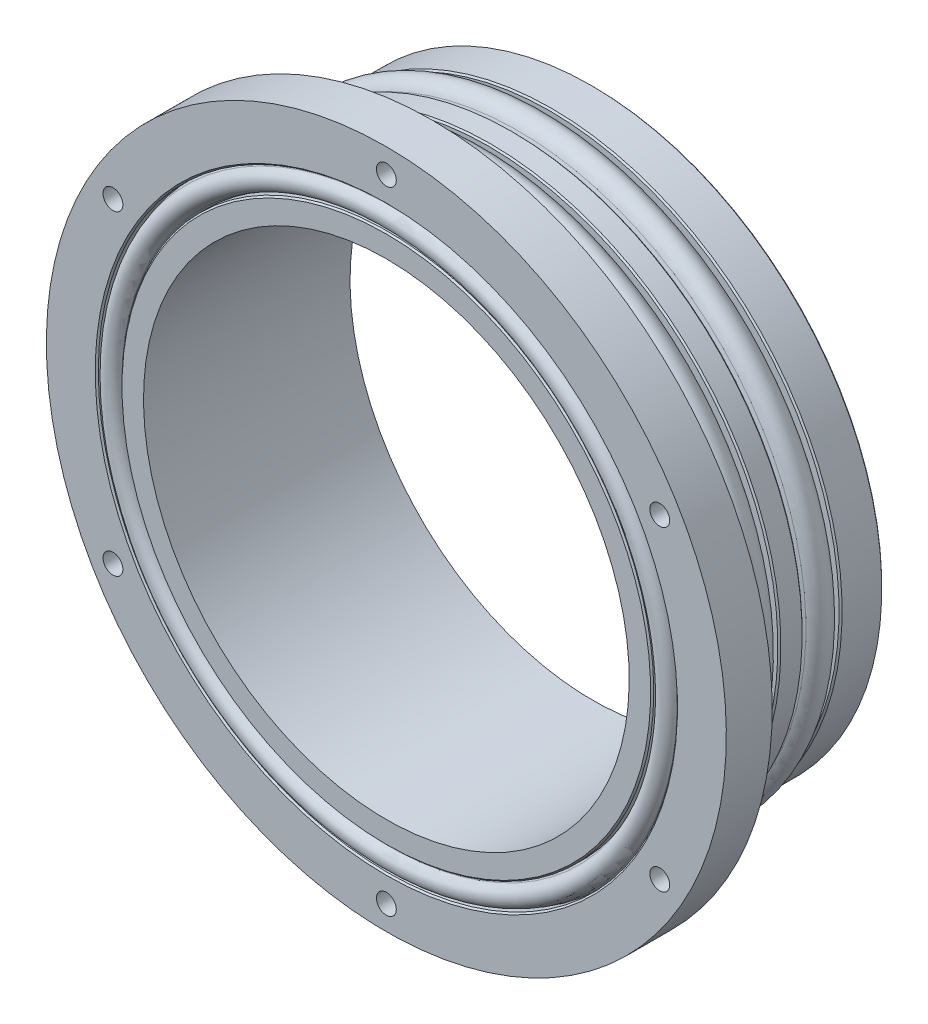
SolidWorks part; units mm, degrees
material "1060 Alloy"
ref_plane "Front Plane" through (0, 0, 0) normal (0, 0, 1) x (1, 0, 0)
ref_plane "Top Plane" through (0, 0, 0) normal (0, 1, 0) x (1, 0, 0)
ref_plane "Right Plane" through (0, 0, 0) normal (1, 0, 0) x (0, 0, -1)
sketch "Sketch1" plane through (0, 0, 0) normal (1, 0, 0) x (0, 0, -1)
  line L0 (0, 0) -> (0, 38.227) construction
  line L1 (0, 37.973) -> (-5.587, 37.973)
  line L2 (-21, 37.973) -> (-21, 44.45)
  line L3 (-21, 44.45) -> (-27, 44.45)
  line L4 (-27, 44.45) -> (-27, 37.8587)
  line L5 (-27, 31.75) -> (0, 31.75)
  line L6 (0, 31.75) -> (0, 37.973)
  line L7 (-18.413, 37.973) -> (-21, 37.973)
  line L8 (-10.413, 37.973) -> (-13.587, 37.973)
  line L9 (0, 0) -> (-27, 0) construction
  line L10 (-27, 0) -> (-27, 31.75) construction
  line L11 (-18.413, 37.973) -> (-18.413, 35.2806)
  line L12 (-18.413, 35.2806) -> (-13.587, 35.2806)
  line L13 (-13.587, 35.2806) -> (-13.587, 37.973)
  line L14 (-10.413, 37.973) -> (-10.413, 35.2806)
  line L15 (-10.413, 35.2806) -> (-5.587, 35.2806)
  line L16 (-5.587, 35.2806) -> (-5.587, 37.973)
  line L17 (0, 38.227) -> (-21, 38.227) construction
  line L18 (-16, 38.227) -> (-16, 38.8112) construction
  line L19 (-21, 37.973) -> (0, 37.973) construction
  line L20 (-27, 34.7599) -> (-24.9426, 34.7599)
  line L21 (-24.9426, 34.7599) -> (-24.9426, 37.8587)
  line L22 (-24.9426, 37.8587) -> (-27, 37.8587)
  line L23 (-27, 34.7599) -> (-27, 31.75)
  line L24 (0, 36.3615) -> (-4, 36.3615) construction
  line L25 (-4, 36.3615) -> (-4, 33.3615) construction
  line L26 (-4, 33.3615) -> (0, 33.3615) construction
  line L27 (-4, 34.8615) -> (0, 34.8615) construction
  circle A0 centre (-16, 37.0459) radius 1.7653 construction
  circle A1 centre (-8, 37.0459) radius 1.7653 construction
  point P2 (-8, 35.2806)
  point P21 (-16, 35.2806)
  dimension "D4" = 3.5306
  dimension "D12" = 2.6924
  dimension "D1" = 38.227
  dimension "D2" = 75.946
  dimension "D3" = 31.75
  dimension "D5" = 21
  dimension "D6" = 6
  dimension "D7" = 88.9
  dimension "D8" = 4.826
  dimension "D9" = 8
  dimension "D10" = 8
  dimension "D11" = 70.5612
  dimension "D13" = 2.0574
  dimension "D14" = 37.973
  dimension "D15" = 2.9464
  dimension "D16" = 0
  dimension "D17" = 0.508
  dimension "D18" = 70.5612
  dimension "D19" = 3.0988
  dimension "D20" = 69.5198
  dimension "D21" = 3.0099
  dimension "D22" = 3
  dimension "D23" = 4
revolve "Revolve1" add sketch "Sketch1" angle 360 about L9
sketch "Sketch2" plane through (0, 0, 27) normal (0, 0, 1) x (1, 0, 0)
  circle A0 centre (0, 41.275) radius 1.3
  circle A1 centre (0, 0) radius 44.45 construction
  circle A2 centre (35.7452, 20.6375) radius 1.3
  circle A3 centre (35.7452, -20.6375) radius 1.3
  circle A4 centre (0, -41.275) radius 1.3
  circle A5 centre (-35.7452, -20.6375) radius 1.3
  circle A6 centre (-35.7452, 20.6375) radius 1.3
  point P17 (0, 0)
  dimension "D1" = 2.6
  dimension "D2" = 3.175
  dimension "D3" = 6
extrude "Cut-Extrude1" cut sketch "Sketch2" against normal up to surface (6 mm away) up to face at (0, 44.45, 21)
chamfer "Chamfer1" distance 0.2 angle 45 7 edges at (0, 37.973, 18.413) (0, 37.973, 5.587) (0, 37.973, 10.413) (0, 37.973, 13.587) (0, 37.973, 0) (0, 37.8587, 27) (0, 34.7599, 27)
sketch "Sketch3" plane through (0, 0, 0) normal (0, 0, -1) x (-1, 0, 0)
  line L0 (-34.29, 0) -> (0, 0) construction
  line L1 (0, 0) -> (0, 34.29) construction
  line L2 (0, 0) -> (34.29, 0) construction
  line L3 (0, -34.29) -> (0, 0) construction
  circle A0 centre (-34.29, 0) radius 1.3
  circle A1 centre (0, 34.29) radius 1.3
  circle A2 centre (34.29, 0) radius 1.3
  circle A3 centre (0, -34.29) radius 1.3
  circle A4 centre (-34.29, 0) radius 2.75 construction
  dimension "D2" = 5.5
  dimension "D3" = 2.6
  dimension "D1" = 68.58
extrude "Cut-Extrude2" cut sketch "Sketch3" against normal blind 4
sketch "Sketch4" plane through (0, 0, 0) normal (1, 0, 0) x (0, 0, -1)
  line L0 (-18.413, 36.0426) -> (-13.587, 36.0426) construction
  line L1 (-13.587, 36.0426) -> (-14.2347, 37.626)
  line L2 (-14.2347, 37.626) -> (-17.7653, 37.626) construction
  line L3 (-17.7653, 37.626) -> (-18.413, 36.0426)
  line L4 (-16, 38.8112) -> (-16, 36.0426) construction
  line L5 (-18.413, -37.773) -> (-18.413, 37.773) construction
  line L6 (-13.587, 37.773) -> (-13.587, -37.773) construction
  line L7 (-18.413, 36.0426) -> (-18.413, 35.2806)
  line L8 (-18.413, -35.2806) -> (-18.413, 35.2806) construction
  line L9 (-18.413, 35.2806) -> (-13.587, 35.2806)
  line L10 (-13.587, 35.2806) -> (-13.587, 36.0426)
  line L11 (-5.587, 37.773) -> (-5.587, -37.773) construction
  line L12 (-10.413, 36.0426) -> (-5.587, 36.0426) construction
  line L13 (-5.587, 36.0426) -> (-6.2347, 37.626)
  line L14 (-6.2347, 37.626) -> (-9.7653, 37.626) construction
  line L15 (-9.7653, 37.626) -> (-10.413, 36.0426)
  line L16 (-8, 38.8112) -> (-8, 36.0426) construction
  line L17 (-10.413, 36.0426) -> (-10.413, 35.2806)
  line L18 (-10.413, 35.2806) -> (-5.587, 35.2806)
  line L19 (-5.587, 35.2806) -> (-5.587, 36.0426)
  line L20 (-5.587, 35.2806) -> (-5.587, -35.2806) construction
  line L21 (-10.413, -37.773) -> (-10.413, 37.773) construction
  line L22 (-5.587, 35.2806) -> (-10.413, 35.2806) construction
  line L23 (-24.9426, 37.8901) -> (-25.7046, 37.8901)
  line L24 (-24.9426, 37.8587) -> (-24.9426, -37.8587) construction
  line L25 (-25.7046, 37.8901) -> (-26.5941, 37.615)
  line L26 (-26.5941, 37.615) -> (-26.5941, 34.9988) construction
  line L27 (-26.5941, 34.9988) -> (-25.7046, 34.7237)
  line L28 (-25.7046, 34.7237) -> (-24.9426, 34.7237)
  line L29 (-24.9426, 34.7237) -> (-24.9426, 37.8901)
  line L30 (-25.7046, 34.7237) -> (-25.7046, 37.8901) construction
  line L31 (-24.9426, 34.7599) -> (-24.9426, -34.7599) construction
  line L32 (-26.5941, 36.3069) -> (-24.9426, 36.3069) construction
  line L33 (0, 0) -> (-27, 0) construction
  line L34 (-27, 31.75) -> (-27, -31.75) construction
  arc A0 (-17.7653, 37.626) -> (-14.2347, 37.626) centre (-16, 36.9039) cw
  arc A1 (-9.7653, 37.626) -> (-6.2347, 37.626) centre (-8, 36.9039) cw
  arc A2 (-26.5941, 34.9988) -> (-26.5941, 37.615) centre (-26.1896, 36.3069) cw
  dimension "D1" = 3.5306
  dimension "D2" = 3.5306
  dimension "D3" = 0.762
  dimension "D4" = 3.5306
  dimension "D5" = 3.5306
  dimension "D6" = 0.762
  dimension "D7" = 2.6162
  dimension "D8" = 2.6162
revolve "Revolve2" add sketch "Sketch4" angle 360 about L33
